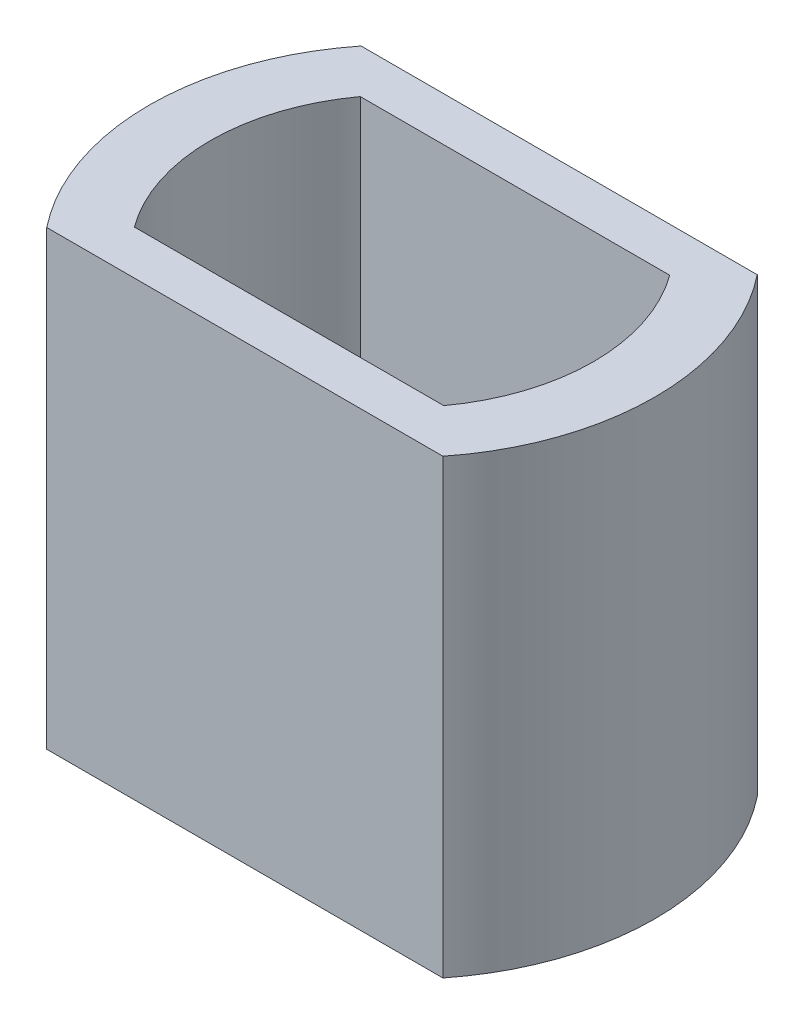
SolidWorks part; units mm, degrees
ref_plane "Front Plane" through (0, 0, 0) normal (0, 0, 1) x (1, 0, 0)
ref_plane "Top Plane" through (0, 0, 0) normal (0, 1, 0) x (1, 0, 0)
ref_plane "Right Plane" through (0, 0, 0) normal (1, 0, 0) x (0, 0, -1)
sketch "Sketch1" plane through (0, 0, 0) normal (0, 1, 0) x (1, 0, 0)
  line L0 (-2.4765, -2.032) -> (2.4765, -2.032)
  line L1 (2, -1.4605) -> (-2, -1.4605)
  line L2 (-2.5332, 2.032) -> (2.4198, 2.032)
  line L3 (2, 1.4605) -> (-2, 1.4605)
  line L4 (-2.4765, -2.032) -> (-2.5607, -2.032)
  line L5 (2.4765, -2.032) -> (2.5607, -2.032)
  line L6 (-2.5332, 2.032) -> (-2.5607, 2.032)
  line L7 (2.4198, 2.032) -> (2.5607, 2.032)
  arc A0 (-2, 1.4605) -> (-2, -1.4605) centre (0, 0) ccw
  arc A1 (2, -1.4605) -> (2, 1.4605) centre (0, 0) ccw
  arc A2 (-2.5607, 2.032) -> (-2.5607, -2.032) centre (0, 0) ccw
  arc A3 (2.5607, -2.032) -> (2.5607, 2.032) centre (0, 0) ccw
  point P1 (-2, 1.4605)
  point P7 (-2, 1.4605)
  point P8 (-2, 1.4605)
  point P9 (-2, 1.4605)
  point P10 (-2.4765, 0)
  point P11 (2.4765, 0)
  dimension "D1" = 4.953
  dimension "D3" = 0.7925
  dimension "D2" = 2.921
  dimension "D4" = 0.5715
  dimension "D5" = 0.5715
extrude "Boss-Extrude1" add sketch "Sketch1" along normal blind 5.842
